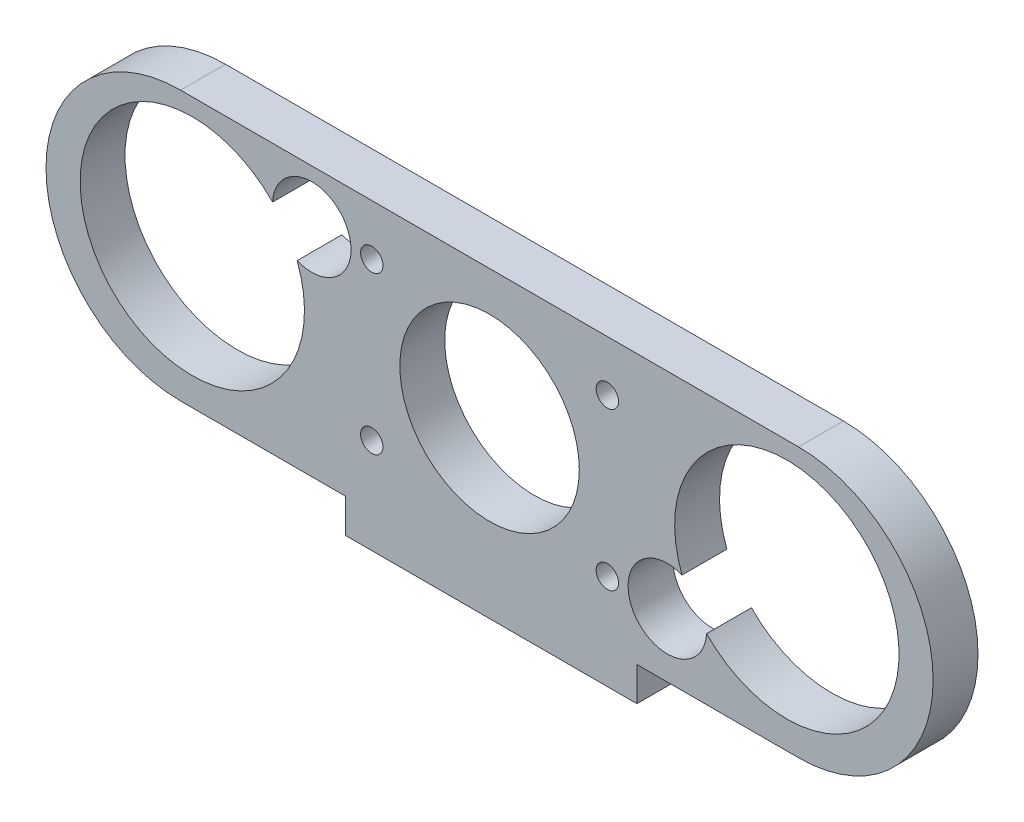
SolidWorks part; units mm, degrees
ref_plane "Front Plane" through (0, 0, 0) normal (0, 0, 1) x (1, 0, 0)
ref_plane "Top Plane" through (0, 0, 0) normal (0, 1, 0) x (1, 0, 0)
ref_plane "Right Plane" through (0, 0, 0) normal (1, 0, 0) x (0, 0, -1)
sketch "Sketch2" plane through (0, 0, 0) normal (0, 0, 1) x (1, 0, 0)
  line L1 (8.9736, 15.851) -> (8.9736, 27.3791) construction
  line L2 (-18.568, 27.3791) -> (36.5153, 27.3791)
  line L3 (36.5153, 3.3791) -> (22.1101, 3.3791)
  line L4 (-3.8899, 3.3791) -> (-3.8899, 0.351)
  line L5 (-3.8899, 0.351) -> (22.1101, 0.351)
  line L6 (22.1101, 0.351) -> (22.1101, 3.3791)
  line L10 (-3.8899, 3.3791) -> (-18.568, 3.3791)
  arc A0 (-18.568, 27.3791) -> (-18.568, 3.3791) centre (-18.568, 15.3791) ccw
  arc A1 (36.5153, 27.3791) -> (36.5153, 3.3791) centre (36.5153, 15.3791) cw
  arc A2 (-10.3711, 22.8369) -> (-8.1817, 19.4115) centre (-17.5264, 15.851) ccw
  arc A3 (28.3184, 8.8651) -> (26.129, 12.2906) centre (35.4736, 15.851) ccw
  arc A4 (-8.1817, 19.4115) -> (-10.3711, 22.8369) centre (-6.8756, 22.6587) ccw
  arc A5 (26.129, 12.2906) -> (28.3184, 8.8651) centre (24.8229, 9.0434) ccw
  circle A6 centre (-1.5264, 22.851) radius 1
  circle A7 centre (19.4736, 22.851) radius 1
  circle A8 centre (-1.5264, 8.851) radius 1
  circle A9 centre (19.4736, 8.851) radius 1
  circle A10 centre (8.9736, 15.851) radius 8
  dimension "D2" = 12
  dimension "D3" = 10.6507
  dimension "D1" = 7
  dimension "D4" = 7
  dimension "D5" = 10.6507
extrude "Boss-Extrude2" add sketch "Sketch2" along normal blind 4
